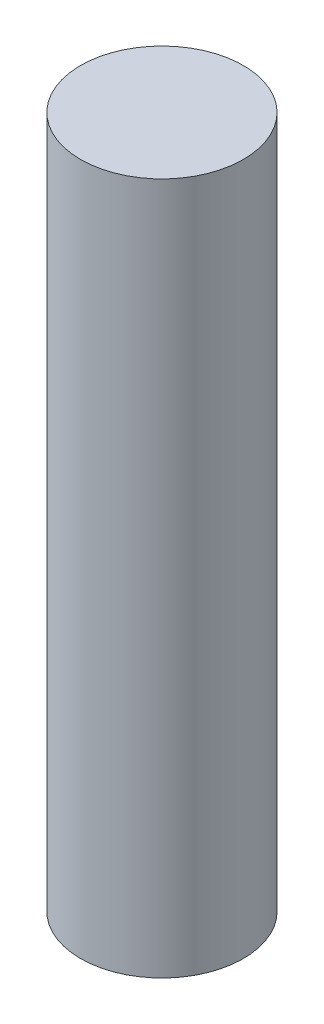
SolidWorks part; units mm, degrees
ref_plane "Front Plane" through (0, 0, 0) normal (0, 0, 1) x (1, 0, 0)
ref_plane "Top Plane" through (0, 0, 0) normal (0, 1, 0) x (1, 0, 0)
ref_plane "Right Plane" through (0, 0, 0) normal (1, 0, 0) x (0, 0, -1)
sketch "Sketch1" plane through (0, 0, 0) normal (0, 1, 0) x (1, 0, 0)
  circle A0 centre (0, 0) radius 2
  dimension "D1" = 4
extrude "Boss-Extrude1" add sketch "Sketch1" along normal blind 17
